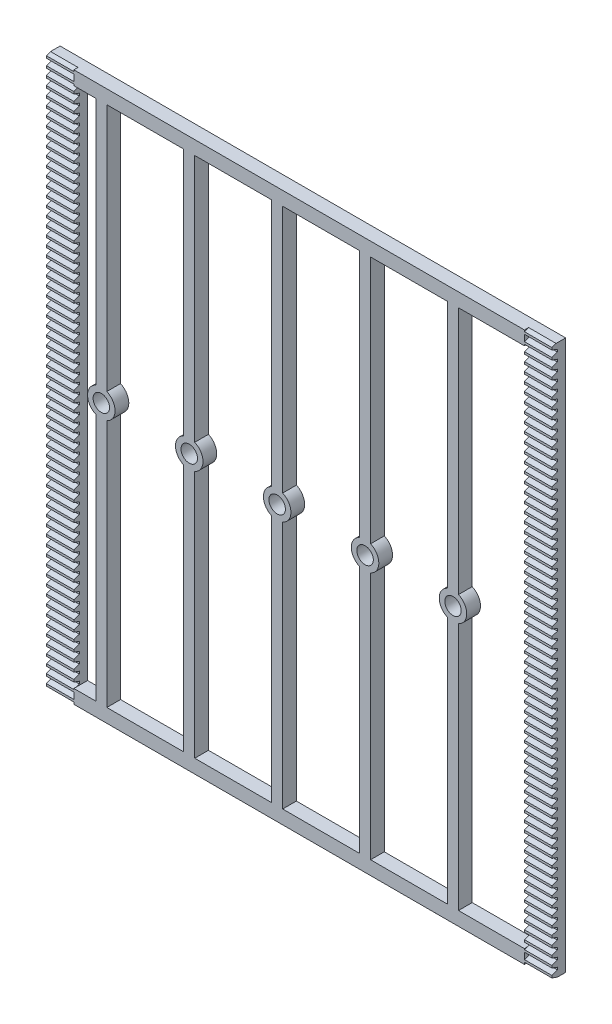
SolidWorks part; units mm, degrees
ref_plane "Front Plane" through (0, 0, 0) normal (0, 0, 1) x (1, 0, 0)
ref_plane "Top Plane" through (0, 0, 0) normal (0, 1, 0) x (1, 0, 0)
ref_plane "Right Plane" through (0, 0, 0) normal (1, 0, 0) x (0, 0, -1)
sketch "Sketch1" plane through (0, 0, 0) normal (0, 0, 1) x (1, 0, 0)
  line L1 (92, 100) -> (-92, 100)
  line L2 (92, 100) -> (92, -100)
  line L3 (92, -100) -> (-92, -100)
  line L4 (-92, 100) -> (-92, -100)
  line L5 (92, 100) -> (-92, -100) construction
  line L6 (92, -100) -> (-92, 100) construction
  point P0 (0, 0)
  dimension "D1" = 184
  dimension "D2" = 200
extrude "Boss-Extrude1" add sketch "Sketch1" along normal blind 5
sketch "Sketch2" plane through (0, 0, 5) normal (0, 0, 1) x (1, 0, 0)
  line L1 (-82, 95) -> (82, 95)
  line L2 (-82, 95) -> (-82, -95)
  line L3 (-82, -95) -> (82, -95)
  line L4 (82, 95) -> (82, -95)
  line L5 (-82, 95) -> (82, -95) construction
  line L6 (-82, -95) -> (82, 95) construction
  point P0 (0, 0)
  dimension "D1" = 164
  dimension "D2" = 190
extrude "Cut-Extrude1" cut sketch "Sketch2" against normal blind 5
sketch "Sketch3" plane through (0, 0, 0) normal (0, 0, 1) x (1, 0, 0)
  line L0 (-82, 95) -> (-82, -95) construction
  line L1 (-82, -95) -> (82, -95) construction
  line L2 (-74, -95) -> (-74, -4.5826)
  line L3 (82, 95) -> (-82, 95) construction
  line L4 (-74, 95) -> (-70, 95)
  line L5 (-70, 95) -> (-70, 4.5826)
  line L6 (-70, -95) -> (-74, -95)
  line L7 (-74, 4.5826) -> (-74, 95)
  line L8 (-70, -4.5826) -> (-70, -95)
  arc A0 (-74, 4.5826) -> (-74, -4.5826) centre (-72, 0) ccw
  arc A1 (-70, -4.5826) -> (-70, 4.5826) centre (-72, 0) ccw
  dimension "D4" = 10
  dimension "D1" = 8
  dimension "D2" = 4
  dimension "D3" = 2
  dimension "D5" = 72
extrude "Boss-Extrude2" add sketch "Sketch3" along normal blind 5
sketch "Sketch4" plane through (0, 0, 5) normal (0, 0, 1) x (1, 0, 0)
  circle A0 centre (-72, 0) radius 3
  dimension "D1" = 6
extrude "Cut-Extrude2" cut sketch "Sketch4" against normal through all
sketch "Sketch5" plane through (92, 0, 0) normal (1, 0, 0) x (0, 0, -1)
  line L0 (-3, -97.7441) -> (-5, -98.4721)
  line L1 (-5, -100) -> (-3, -100)
  line L2 (-5, -100) -> (-5, -96.8584)
  line L3 (-5, -96.8584) -> (-3, -96.8584)
  line L4 (-3, -100) -> (-3, -96.8584)
  line L5 (-3, -100) -> (-5, -99.2721)
  line M9 (-5, 100) -> (-5, -100)
  line M10 (-5, -100) -> (0, -100)
  dimension "D1" = 2
  dimension "D2" = 3.1416
  dimension "D3" = 0.8
  dimension "D4" = 20
  dimension "D5" = 20
extrude "Cut-Extrude3" cut sketch "Sketch5" against normal blind 10 contours L5 L2 M10 | L0 L4 L3 M9
pattern_linear "LPattern3" count 64 spacing 3.1416 along (0, 1, 0) of "Cut-Extrude3"
sketch "Sketch6" plane through (-92, 0, 0) normal (-1, 0, 0) x (0, 0, 1)
  line L0 (3, -100) -> (5, -99.2721)
  line L1 (5, -100) -> (3, -100)
  line L2 (5, -100) -> (5, -96.8584)
  line L3 (5, -96.8584) -> (3, -96.8584)
  line L4 (3, -100) -> (3, -96.8584)
  line L5 (5, -98.4721) -> (3, -97.7441)
  line M7 (0, -100) -> (5, -100)
  line M8 (5, -100) -> (5, 100)
  dimension "D1" = 3.1416
  dimension "D2" = 2
  dimension "D3" = 0.8
  dimension "D4" = 20
  dimension "D5" = 20
extrude "Cut-Extrude4" cut sketch "Sketch6" against normal blind 10 contours L0 M7 M8 | L5 L2 L3 L4
pattern_linear "LPattern4" count 64 spacing 3.1416 along (0, 1, 0) of "Cut-Extrude4"
pattern_linear "LPattern5" count 5 spacing 32 along (1, 0, 0) of "Boss-Extrude2", "Cut-Extrude2"
